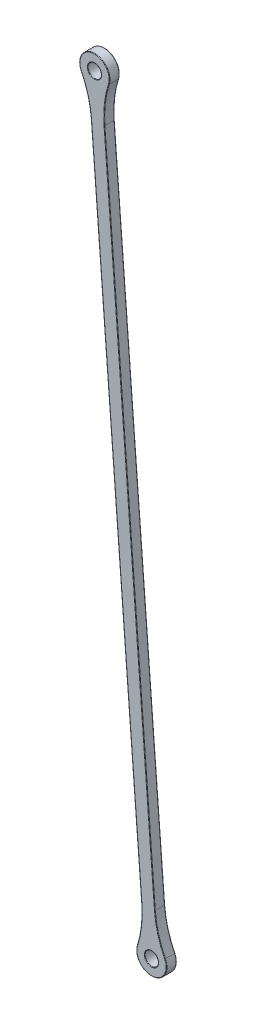
SolidWorks part; units mm, degrees
ref_plane "Front Plane" through (0, 0, 0) normal (0, 0, 1) x (1, 0, 0)
ref_plane "Top Plane" through (0, 0, 0) normal (0, 1, 0) x (1, 0, 0)
ref_plane "Right Plane" through (0, 0, 0) normal (1, 0, 0) x (0, 0, -1)
sketch "Sketch1" plane through (0, 0, 0) normal (0, 0, 1) x (1, 0, 0)
  line L0 (14.5, 81.5) -> (-2.5448, 302.8447) construction
  line L1 (14.5, 81.5) -> (-2.5448, 302.8447) construction
  line L2 (-2.5448, 302.8447) -> (14.5, 81.5) construction
  line L3 (-0.5507, 302.9983) -> (16.4941, 81.6536)
  line L4 (-4.5389, 302.6911) -> (12.5059, 81.3464)
  circle A0 centre (-2.5448, 302.8447) radius 4.5 construction
  circle A1 centre (14.5, 81.5) radius 4.5 construction
  arc A2 (-0.5507, 302.9983) -> (-4.5389, 302.6911) centre (-2.5448, 302.8447) ccw
  arc A3 (12.5059, 81.3464) -> (16.4941, 81.6536) centre (14.5, 81.5) ccw
  arc A4 (16.4941, 81.6536) -> (12.5059, 81.3464) centre (14.5, 81.5) ccw
  arc A5 (-0.5507, 302.9983) -> (-4.5389, 302.6911) centre (-2.5448, 302.8447) cw
  arc A6 (16.1846, 85.6728) -> (12.1964, 85.3657) centre (14.5, 81.5) cw
  arc A7 (-0.2412, 298.979) -> (-4.2294, 298.6719) centre (-2.5448, 302.8447) ccw
  point P4 (5.9776, 192.1723)
  dimension "D1" = 9
  dimension "D2" = 4
extrude "Boss-Extrude1" add sketch "Sketch1" against normal blind 3 contours A6 L3 A3 L4 | L3 A5 L4 A4 | L3 A7 L4 A2
fillet "Fillet1" radius 30 4 edges at (12.1964, 85.3657, -1.5) (16.1846, 85.6728, -1.5) (-4.2294, 298.6719, -1.5) (-0.2412, 298.979, -1.5)
fillet "Fillet2" radius 0.15 20 edges at (-0.5448, 302.8447, -3) (-0.5448, 302.8447, 0) (16.5, 81.5, -3) (16.5, 81.5, 0) (-4.5342, 295.4868, -3) (-4.5342, 295.4868, 0) (3.9835, 192.0188, -3) (3.9835, 192.0188, 0) (11.4075, 88.4665, -3) (11.4075, 88.4665, 0) (14.8455, 77.0133, 0) (14.8455, 77.0133, -3) (16.4894, 88.8579, -3) (16.4894, 88.8579, 0) (7.9717, 192.3259, 0) (7.9717, 192.3259, -3) (0.5477, 295.8782, -3) (0.5477, 295.8782, 0) (-2.8903, 307.3314, -3) (-2.8903, 307.3314, 0)
